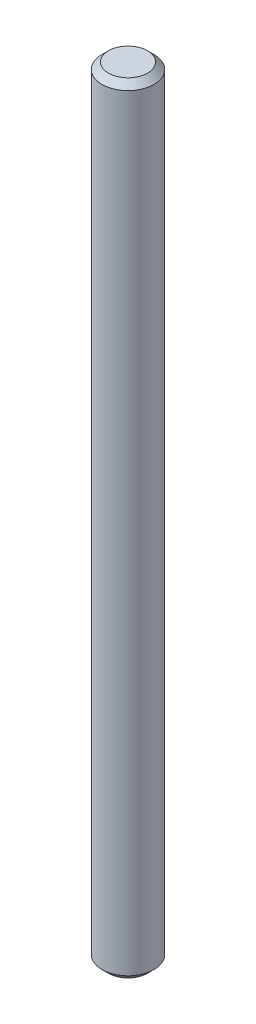
SolidWorks part; units mm, degrees
ref_plane "前基準面" through (0, 0, 0) normal (0, 0, 1) x (1, 0, 0)
ref_plane "上基準面" through (0, 0, 0) normal (0, 1, 0) x (1, 0, 0)
ref_plane "右基準面" through (0, 0, 0) normal (1, 0, 0) x (0, 0, -1)
sketch "草圖1" plane through (0, 0, 0) normal (0, 1, 0) x (1, 0, 0)
  circle A0 centre (0, 0) radius 4
  dimension "D1" = 8
extrude "填料-伸長1" add sketch "草圖1" along normal blind 120
chamfer "導角1" distance 1 angle 45 2 edges at (0, 0, 4) (0, 120, 4)
